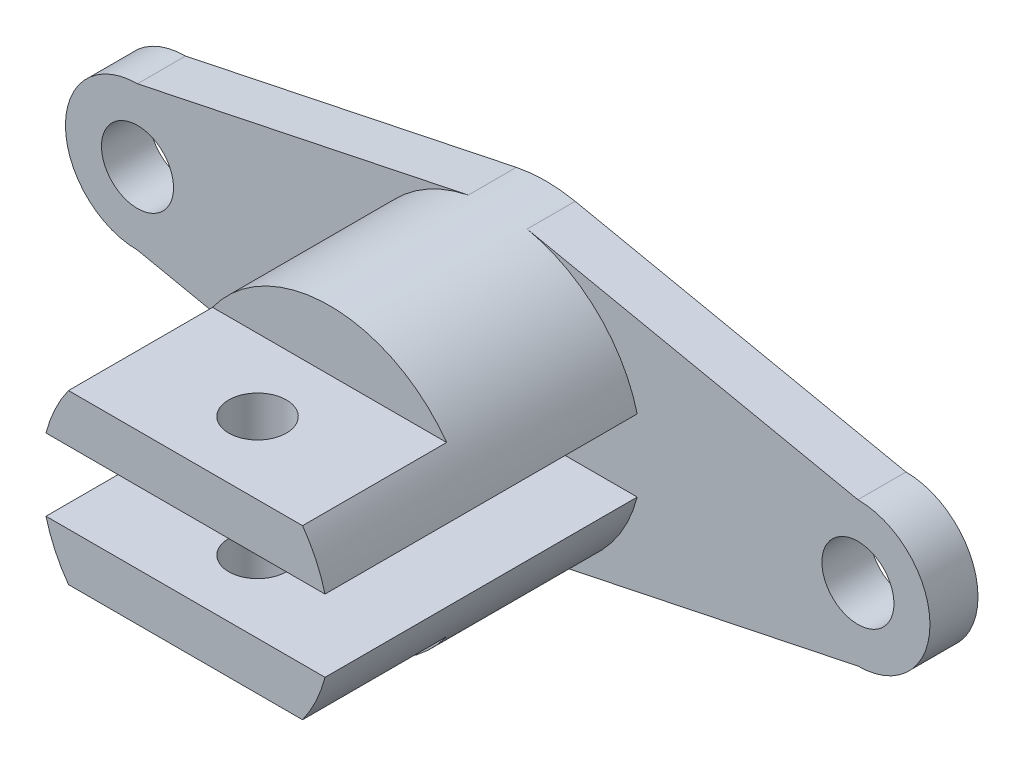
SolidWorks part; units mm, degrees
ref_plane "Front Plane" through (0, 0, 0) normal (0, 0, 1) x (1, 0, 0)
ref_plane "Top Plane" through (0, 0, 0) normal (0, 1, 0) x (1, 0, 0)
ref_plane "Right Plane" through (0, 0, 0) normal (1, 0, 0) x (0, 0, -1)
sketch "Sketch1" plane through (0, 0, 0) normal (0, 0, 1) x (1, 0, 0)
  line L0 (0, 80.331) -> (0, -85.3438) construction
  line L1 (-143.3676, 0) -> (139.3573, 0) construction
  line L2 (-75, 80.331) -> (-75, -85.3438) construction
  line L3 (75, 80.331) -> (75, -85.3438) construction
  line L4 (75, 15) -> (6.1264, 29.3678)
  line L5 (-75, 15) -> (-6.1264, 29.3678)
  line L6 (-75, -15) -> (-6.1264, -29.3678)
  line L7 (75, -15) -> (6.1264, -29.3678)
  arc A0 (-6.1264, -29.3678) -> (6.1264, -29.3678) centre (0, 0) ccw
  arc A1 (-75, 15) -> (-75, -15) centre (-75, 0) ccw
  arc A2 (75, -15) -> (75, 15) centre (75, 0) ccw
  arc A3 (6.1264, 29.3678) -> (-6.1264, 29.3678) centre (0, 0) ccw
  circle A4 centre (75, 0) radius 7.5
  circle A5 centre (-75, 0) radius 7.5
  dimension "D1" = 60
  dimension "D4" = 30
  dimension "D5" = 30
  dimension "D6" = 15
  dimension "D7" = 15
  dimension "D2" = 75
  dimension "D3" = 75
extrude "Boss-Extrude1" add sketch "Sketch1" along normal blind 10
sketch "Sketch2" plane through (0, 0, 10) normal (0, 0, 1) x (1, 0, 0)
  circle A0 centre (0, 0) radius 30
  dimension "D1" = 60
extrude "Boss-Extrude2" add sketch "Sketch2" along normal blind 65
sketch "Sketch3" plane through (0, 0, 75) normal (0, 0, 1) x (1, 0, 0)
  line L0 (-30, 0) -> (30, 0) construction
  line L1 (-29.0474, -7.5) -> (29.0474, -7.5)
  line L2 (-29.0474, 7.5) -> (29.0474, 7.5)
  line L3 (-103.1736, 7.5) -> (115.8071, 7.5) construction
  line L4 (-103.1736, 0) -> (115.8071, 0) construction
  line L5 (-103.1736, -7.5) -> (115.8071, -7.5) construction
  arc A0 (29.0474, -7.5) -> (29.0474, 7.5) centre (0, 0) ccw
  circle A1 centre (0, 0) radius 30
  arc A2 (-29.0474, 7.5) -> (-29.0474, -7.5) centre (0, 0) ccw
  dimension "D1" = 7.5
  dimension "D2" = 7.5
  dimension "D3" = 0
extrude "Cut-Extrude1" cut sketch "Sketch3" against normal blind 65
sketch "Sketch4" plane through (0, 0, 75) normal (0, 0, 1) x (1, 0, 0)
  line L1 (-24.367, -17.5) -> (24.367, -17.5)
  line L2 (-24.367, 17.5) -> (24.367, 17.5)
  arc A0 (29.0474, 7.5) -> (-29.0474, 7.5) centre (0, 0) ccw construction
  arc A1 (24.367, 17.5) -> (-24.367, 17.5) centre (0, 0) ccw
  arc A2 (-29.0474, -7.5) -> (29.0474, -7.5) centre (0, 0) ccw construction
  arc A3 (-24.367, -17.5) -> (24.367, -17.5) centre (0, 0) ccw
extrude "Cut-Extrude2" cut sketch "Sketch4" against normal blind 30
sketch "Sketch7" plane through (0, -17.5, 0) normal (0, -1, 0) x (1, 0, 0)
  line L0 (-6.1264, 0) -> (6.1264, 0) construction
  line L1 (-90, 10) -> (-90, 0) construction
  circle A0 centre (0, 60) radius 6
  dimension "D1" = 12
  dimension "D2" = 60
  dimension "D3" = 90
extrude "Cut-Extrude3" cut sketch "Sketch7" against normal through all both and the other way through all
